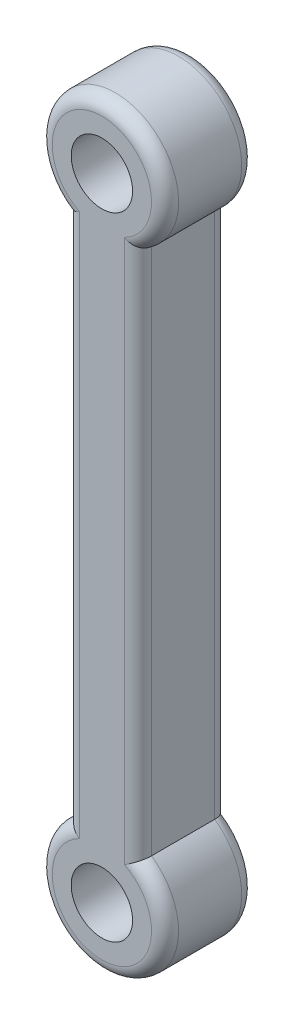
SolidWorks part; units mm, degrees
ref_plane "Alzado" through (0, 0, 0) normal (0, 0, 1) x (1, 0, 0)
ref_plane "Planta" through (0, 0, 0) normal (0, 1, 0) x (1, 0, 0)
ref_plane "Vista lateral" through (0, 0, 0) normal (1, 0, 0) x (0, 0, -1)
sketch "Croquis1" plane through (0, 0, 0) normal (0, 0, 1) x (1, 0, 0)
  line L0 (0, 17.5) -> (0, -17.5) construction
  line L2 (2, -14.6277) -> (2, 14.6277)
  line L4 (-2, -14.6277) -> (-2, 14.6277)
  line L5 (2, -14.6277) -> (-2, 14.6277) construction
  line L6 (2, 14.6277) -> (-2, -14.6277) construction
  arc A0 (-2, -14.6277) -> (2, -14.6277) centre (0, -17.5) ccw
  circle A1 centre (0, -17.5) radius 1.7
  arc A2 (2, 14.6277) -> (-2, 14.6277) centre (0, 17.5) ccw
  circle A3 centre (0, 17.5) radius 1.7
  point P0 (0, 0)
  point P12 (0, -16.6162)
  point P13 (0, 0)
  point P14 (0, 0)
  dimension "D2" = 3.4
  dimension "D3" = 7
  dimension "D1" = 35
  dimension "D4" = 4
extrude "Saliente-Extruir1" add sketch "Croquis1" along normal blind 5
fillet "Redondeo1" radius 0.75 8 edges at (0, 21, 0) (-2, 0, 0) (2, 0, 0) (0, -21, 0) (0, -21, 5) (0, 21, 5) (-2, 0, 5) (2, 0, 5)
